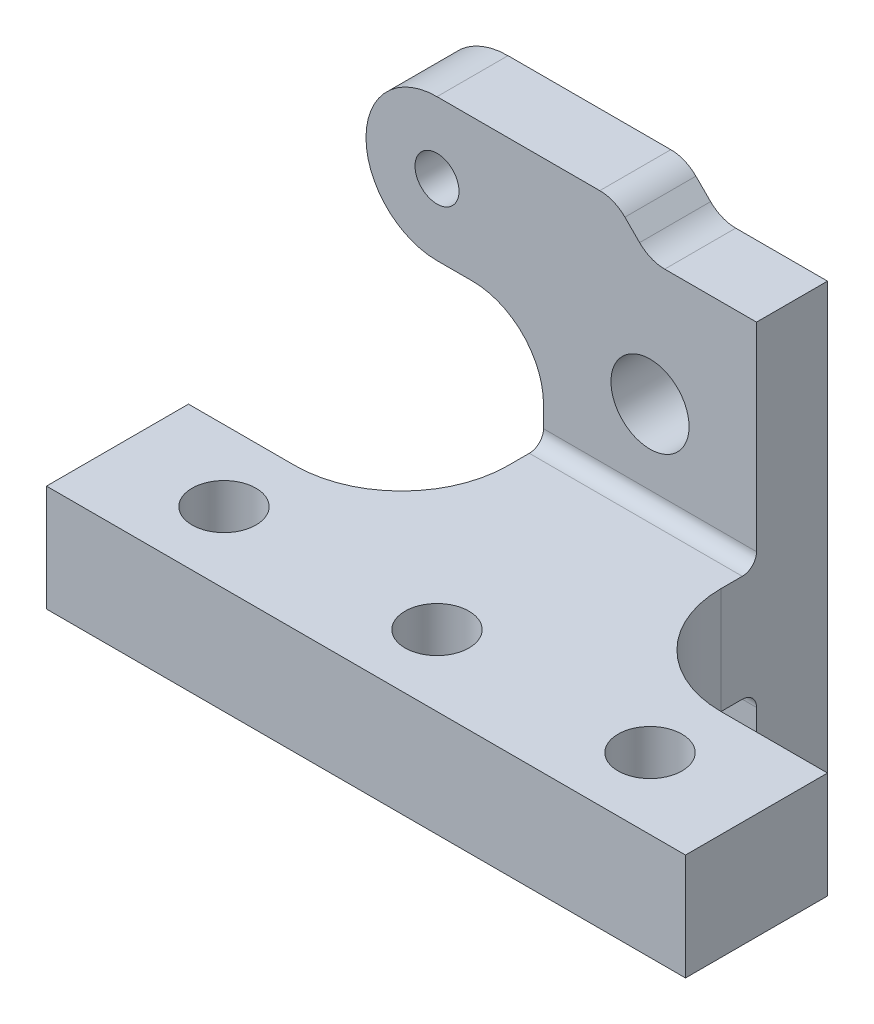
SolidWorks part; units mm, degrees
material "ABS"
ref_plane "前视基准面" through (0, 0, 0) normal (0, 0, 1) x (1, 0, 0)
ref_plane "上视基准面" through (0, 0, 0) normal (0, 1, 0) x (1, 0, 0)
ref_plane "右视基准面" through (0, 0, 0) normal (1, 0, 0) x (0, 0, -1)
sketch "草图1" plane through (0, 0, 0) normal (0, 0, 1) x (1, 0, 0)
  line L0 (0, 0) -> (0, 20) construction
  line L1 (-15, -37.5) -> (15, -37.5)
  line L2 (-15, -37.5) -> (-15, 37.5)
  line L3 (-15, 37.5) -> (15, 37.5)
  line L4 (15, -37.5) -> (15, 37.5)
  line L5 (-15, -37.5) -> (15, 37.5) construction
  line L6 (-15, 37.5) -> (15, -37.5) construction
  line L7 (0, 0) -> (0, -20) construction
  circle A0 centre (0, 20) radius 5.5
  circle A1 centre (0, -20) radius 5.5
  point P0 (0, 0)
  dimension "D3" = 11
  dimension "D4" = 11
  dimension "D1" = 30
  dimension "D2" = 75
extrude "凸台-拉伸1" add sketch "草图1" along normal blind 10
sketch "草图2" plane through (0, 0, 10) normal (0, 0, 1) x (1, 0, 0)
  line L0 (15, -37.5) -> (15, 37.5) construction
  line L1 (-15, 7.5) -> (15, 7.5)
  line L2 (-15, 7.5) -> (-15, -7.5)
  line L3 (-15, -7.5) -> (15, -7.5)
  line L4 (15, 7.5) -> (15, -7.5)
  line L5 (-15, 7.5) -> (15, -7.5) construction
  line L6 (-15, -7.5) -> (15, 7.5) construction
  point P0 (0, 0)
  dimension "D1" = 15
extrude "凸台-拉伸2" add sketch "草图2" along normal blind 40
fillet "圆角1" radius 2 2 edges at (0, 7.5, 10) (0, -7.5, 10)
sketch "草图3" plane through (0, -7.5, 0) normal (0, -1, 0) x (-1, 0, 0)
  line L0 (0, -10) -> (0, -40) construction
  line L1 (-15, -10) -> (15, -10) construction
  circle A0 centre (0, -40) radius 4.5
extrude "切除-拉伸1" cut sketch "草图3" against normal up to vertex (15 mm away)
sketch "草图5" plane through (15, 0, 0) normal (1, 0, 0) x (0, 0, -1)
  line L0 (-50, 7.5) -> (-12, 7.5) construction
  line L1 (-50, -7.5) -> (-30, -7.5)
  line L2 (-50, -7.5) -> (-50, 7.5)
  line L3 (-50, 7.5) -> (-30, 7.5)
  line L4 (-30, -7.5) -> (-30, 7.5)
  line L5 (-40, 7.5) -> (-40, -7.5) construction
  line L6 (-50, 0) -> (-30, 0) construction
  point P64 (-40, 0)
extrude "凸台-拉伸3" add sketch "草图5" along normal blind 30
sketch "草图6" plane through (0, -7.5, 0) normal (0, -1, 0) x (-1, 0, 0)
  line L0 (0, -40) -> (-30, -40) construction
  circle A0 centre (-30, -40) radius 4.5
extrude "切除-拉伸2" cut sketch "草图6" against normal blind 30
fillet "圆角2" radius 15 1 edges at (15, 0, 30)
sketch "草图7" plane through (-15, 0, 0) normal (-1, 0, 0) x (0, 0, 1)
  line L0 (50, -7.5) -> (12, -7.5) construction
  line L1 (50, 7.5) -> (30, 7.5)
  line L2 (50, 7.5) -> (50, -7.5)
  line L3 (50, -7.5) -> (30, -7.5)
  line L4 (30, 7.5) -> (30, -7.5)
  line L5 (40, -7.5) -> (40, 7.5) construction
  line L6 (50, 0) -> (30, 0) construction
  point P88 (40, 0)
extrude "凸台-拉伸4" add sketch "草图7" along normal blind 30
fillet "圆角3" radius 15 1 edges at (-15, 0, 30)
sketch "草图8" plane through (0, -7.5, 0) normal (0, -1, 0) x (-1, 0, 0)
  line L0 (0, -40) -> (30, -40) construction
  circle A0 centre (30, -40) radius 4.5
extrude "切除-拉伸3" cut sketch "草图8" against normal blind 30
sketch "草图9" plane through (0, 0, 10) normal (0, 0, 1) x (1, 0, 0)
  line L0 (-30, 42.5) -> (-5, 42.5)
  line L2 (15, 37.5) -> (-15, 37.5) construction
  line L3 (-30, 22.5) -> (-15, 22.5)
  line L4 (-15, 37.5) -> (-15, 9.5) construction
  line L5 (0, 37.5) -> (-15, 22.5)
  line L7 (-5, 42.5) -> (0, 37.5)
  arc A0 (-30, 42.5) -> (-30, 22.5) centre (-30, 32.5) ccw
extrude "凸台-拉伸5" add sketch "草图9" against normal blind 10
fillet "圆角4" radius 5 2 edges at (-5, 42.5, 5) (0, 37.5, 5)
fillet "圆角5" radius 10 1 edges at (-15, 22.5, 5)
sketch "草图10" plane through (0, 0, 10) normal (0, 0, 1) x (1, 0, 0)
  circle A0 centre (-30, 32.5) radius 3.1
extrude "切除-拉伸4" cut sketch "草图10" against normal blind 10
